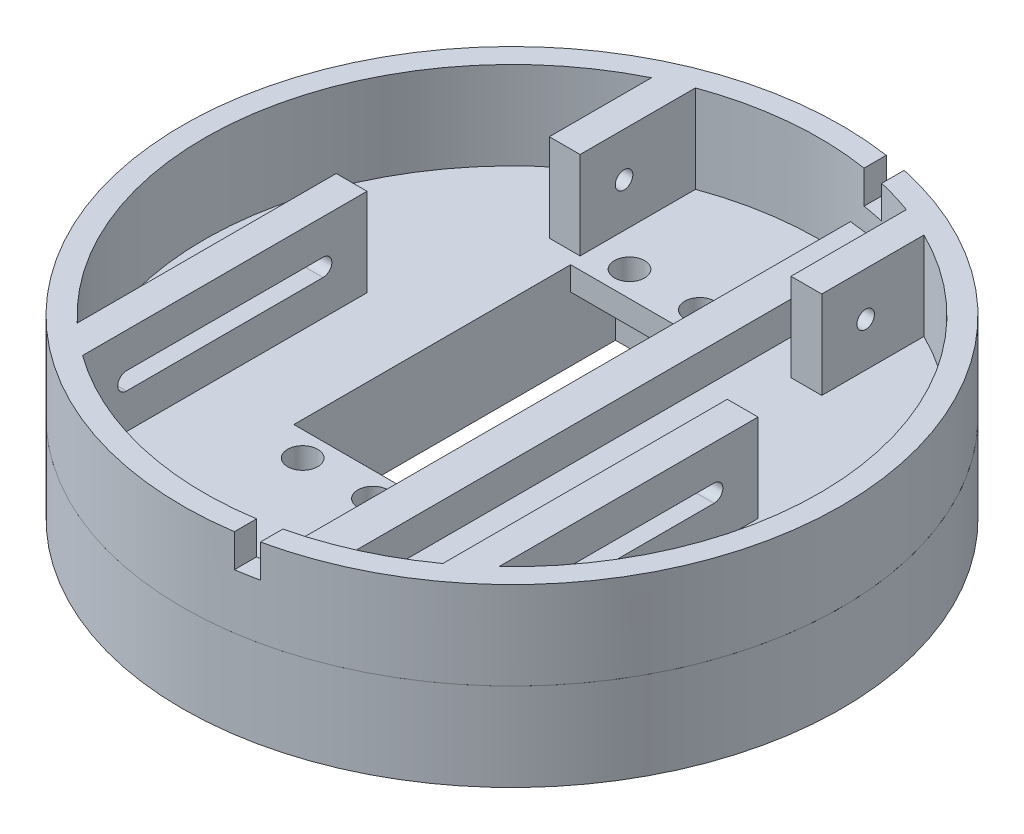
SolidWorks part; units mm, degrees
material "Polylactic Acid (PLA)"
ref_plane "Front Plane" through (0, 0, 0) normal (0, 0, 1) x (1, 0, 0)
ref_plane "Top Plane" through (0, 0, 0) normal (0, 1, 0) x (1, 0, 0)
ref_plane "Right Plane" through (0, 0, 0) normal (1, 0, 0) x (0, 0, -1)
sketch "Sketch1" plane through (0, 0, 0) normal (0, 1, 0) x (1, 0, 0)
  circle A0 centre (0, 0) radius 47.625
  dimension "D1" = 95.25
extrude "Boss-Extrude1" add sketch "Sketch1" against normal blind 12.7
sketch "Sketch2" plane through (0, 0, 0) normal (0, 1, 0) x (1, 0, 0)
  line L0 (0, -50.8) -> (0, 44.45) construction
  line L11 (26.035, 5.08) -> (26.035, -36.0275)
  line L12 (-30.48, 5.08) -> (-26.035, 5.08)
  line L14 (19.685, 25.0825) -> (15.24, 25.0825)
  line L15 (15.24, 25.0825) -> (15.24, 41.7558)
  line L16 (-30.48, 5.08) -> (-30.48, -32.3539)
  line L18 (-19.685, 25.0825) -> (-19.685, 39.8535)
  line L19 (19.685, 25.0825) -> (19.685, 39.8535)
  line L20 (-15.24, 25.0825) -> (-15.24, 41.7558)
  line L21 (-19.685, 25.0825) -> (-15.24, 25.0825)
  line L22 (-26.035, 5.08) -> (-26.035, -36.0275)
  line L23 (30.48, 5.08) -> (30.48, -32.3539)
  line L27 (30.48, 5.08) -> (26.035, 5.08)
  circle A2 centre (0, 0) radius 47.625
  circle A6 centre (0, 0) radius 44.45
  dimension "D1" = 88.9
  dimension "D8" = 95.25
  dimension "D2" = 6.35
  dimension "D3" = 4.445
  dimension "D4" = 4.445
  dimension "D5" = 26.035
  dimension "D6" = 5.08
  dimension "D7" = 20.0025
extrude "Boss-Extrude4" add sketch "Sketch2" along normal blind 12.7 separate body
sketch "Sketch8" plane through (-15.24, 0, 0) normal (-1, 0, 0) x (0, 0, 1)
  line L0 (-25.0825, 12.7) -> (-41.7558, 12.7) construction
  line L1 (-25.0825, 12.7) -> (-25.0825, 0) construction
  circle A0 centre (-31.4325, 6.35) radius 1.27
  dimension "D1" = 6.35
  dimension "D3" = 2.54
  dimension "D2" = 6.35
extrude "Cut-Extrude8" cut sketch "Sketch8" against normal up to next
sketch "Sketch17" plane through (-26.035, 0, 0) normal (1, 0, 0) x (0, 0, -1)
  line L0 (-29.6775, 6.35) -> (-1.27, 6.35) construction
  line L1 (-29.6775, 7.62) -> (-1.27, 7.62)
  line L2 (-29.6775, 5.08) -> (-1.27, 5.08)
  line L3 (-36.0275, 12.7) -> (-36.0275, 0) construction
  line L4 (5.08, 0) -> (-36.0275, 0) construction
  line L8 (5.08, 12.7) -> (5.08, 0) construction
  arc A0 (-29.6775, 7.62) -> (-29.6775, 5.08) centre (-29.6775, 6.35) ccw
  arc A1 (-1.27, 5.08) -> (-1.27, 7.62) centre (-1.27, 6.35) ccw
  point P2 (-15.4738, 6.35)
  dimension "D3" = 1.27
  dimension "D1" = 6.35
  dimension "D2" = 6.35
  dimension "D4" = 6.35
extrude "Cut-Extrude15" cut sketch "Sketch17" against normal up to next (4.445 mm away)
mirror "Mirror4" about plane through (0, 0, 0) normal (1, 0, 0) of "Cut-Extrude8", "Cut-Extrude15"
sketch "Sketch10" plane through (0, 0, 0) normal (0, 1, 0) x (1, 0, 0)
  line L0 (3.81, 44.2864) -> (3.81, -44.2864) construction
  line L2 (10.16, -43.2733) -> (10.16, 43.2733)
  line L3 (4.7625, -44.1941) -> (4.7625, 44.1941)
  arc A1 (10.16, 43.2733) -> (3.81, 44.2864) centre (0, 0) ccw
  arc A2 (3.81, -44.2864) -> (10.16, -43.2733) centre (0, 0) ccw
  dimension "D2" = 3.81
  dimension "D1" = 88.9
  dimension "D3" = 6.35
  dimension "D4" = 0.9525
extrude "Boss-Extrude5" add sketch "Sketch10" along normal blind 4.7625 separate body
sketch "Sketch12" plane through (0, 12.7, 0) normal (0, 1, 0) x (1, 0, 0)
  line L0 (3.81, 50.6569) -> (3.81, -47.4724) construction
  line L1 (10.16, -46.5286) -> (10.16, 46.5286)
  line L3 (6.985, 47.11) -> (6.985, -47.11)
  arc A0 (10.16, 46.5286) -> (6.985, 47.11) centre (0, 0) ccw
  arc A1 (6.985, -47.11) -> (10.16, -46.5286) centre (0, 0) ccw
  dimension "D3" = 6.985
  dimension "D2" = 95.25
  dimension "D1" = 6.35
  dimension "D5" = 3.175
extrude "Cut-Extrude10" cut sketch "Sketch12" against normal blind 4.7625
sketch "Sketch13" plane through (0, 0, 0) normal (0, 1, 0) x (1, 0, 0)
  line L0 (3.81, -59.065) -> (3.81, 65.3266) construction
  circle A2 centre (-4.9213, 13.5255) radius 8.7312 construction
  circle A3 centre (-4.9213, 13.5255) radius 9.525 construction
  dimension "D2" = 17.4625
  dimension "D3" = 19.05
  dimension "D1" = 3.81
  dimension "D4" = 8.4455
sketch "Sketch14" plane through (0, -12.7, 0) normal (0, -1, 0) x (1, 0, 0)
  line L0 (4.9847, -13.5255) -> (-14.8272, -13.5255) construction
  line L2 (4.9848, -29.7815) -> (-14.8272, -29.7815)
  line L3 (4.9848, -29.7815) -> (4.9847, 23.1775)
  line L4 (4.9847, 23.1775) -> (-14.8272, 23.1775)
  line L5 (-14.8272, -29.7815) -> (-14.8272, 23.1775)
  point P4 (-4.9213, -13.5255)
  dimension "D1" = 52.959
  dimension "D2" = 19.812
  dimension "D3" = 16.256
extrude "Cut-Extrude11" cut sketch "Sketch14" against normal blind 9.2758
sketch "Sketch15" plane through (0, -3.4242, 0) normal (0, -1, 0) x (1, 0, 0)
  line L0 (4.9848, -29.7815) -> (4.9847, 23.1775) construction
  line L1 (4.9848, -23.3045) -> (-14.8272, -23.3045)
  line L2 (4.9848, -23.3045) -> (4.9848, 16.7005)
  line L3 (4.9848, 16.7005) -> (-14.8272, 16.7005)
  line L4 (-14.8272, -23.3045) -> (-14.8272, 16.7005)
  line L5 (-14.8272, 23.1775) -> (-14.8272, -29.7815) construction
  line L6 (4.9847, 23.1775) -> (-14.8272, 23.1775) construction
  line L7 (-14.8272, -29.7815) -> (4.9848, -29.7815) construction
  dimension "D1" = 6.477
  dimension "D2" = 6.477
extrude "Cut-Extrude12" cut sketch "Sketch15" against normal up to surface (8.1867 mm away)
sketch "Sketch16" plane through (0, -3.4242, 0) normal (0, -1, 0) x (1, 0, 0)
  line L0 (-14.8272, -26.9875) -> (4.9847, -26.9875) construction
  line L1 (-14.8272, -23.3045) -> (-14.8272, -29.7815) construction
  line L2 (4.9848, -29.7815) -> (4.9847, 23.1775) construction
  line L3 (-14.8272, 20.2565) -> (4.9847, 20.2565) construction
  line L4 (-14.8272, 23.1775) -> (-14.8272, 16.7005) construction
  line L5 (-4.9213, -26.9875) -> (-4.9213, 20.2565) construction
  circle A0 centre (-10.0013, -26.9875) radius 2.1844
  circle A1 centre (0.1587, -26.9875) radius 2.1844
  circle A2 centre (-10.0013, 20.2565) radius 2.1844
  circle A3 centre (0.1587, 20.2565) radius 2.1844
  dimension "D7" = 4.3688
  dimension "D8" = 4.3688
  dimension "D9" = 4.3688
  dimension "D10" = 4.3688
  dimension "D1" = 13.462
  dimension "D2" = 33.782
  dimension "D3" = 5.08
  dimension "D4" = 5.08
  dimension "D5" = 5.08
  dimension "D6" = 5.08
extrude "Cut-Extrude13" cut sketch "Sketch16" against normal up to surface (3.4242 mm away)
